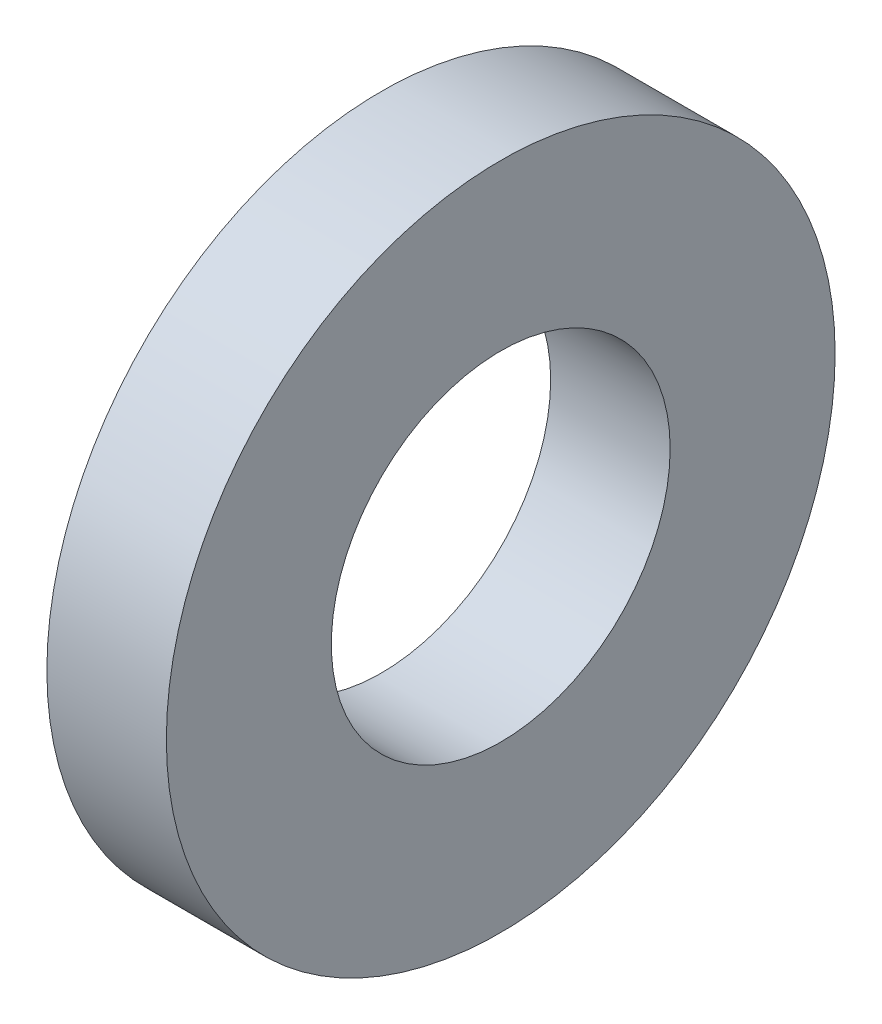
SolidWorks part; units mm, degrees
ref_plane "Front Plane" through (0, 0, 0) normal (0, 0, 1) x (1, 0, 0)
ref_plane "Top Plane" through (0, 0, 0) normal (0, 1, 0) x (1, 0, 0)
ref_plane "Right Plane" through (0, 0, 0) normal (1, 0, 0) x (0, 0, -1)
sketch "Sketch1" plane through (0, 0, 0) normal (1, 0, 0) x (0, 0, -1)
  circle A0 centre (0, 0) radius 2.413
  circle A1 centre (0, 0) radius 4.7625
  dimension "OD" = 4.826
  dimension "ID" = 9.525
extrude "Boss-Extrude1" add sketch "Sketch1" along normal blind 1.7018
